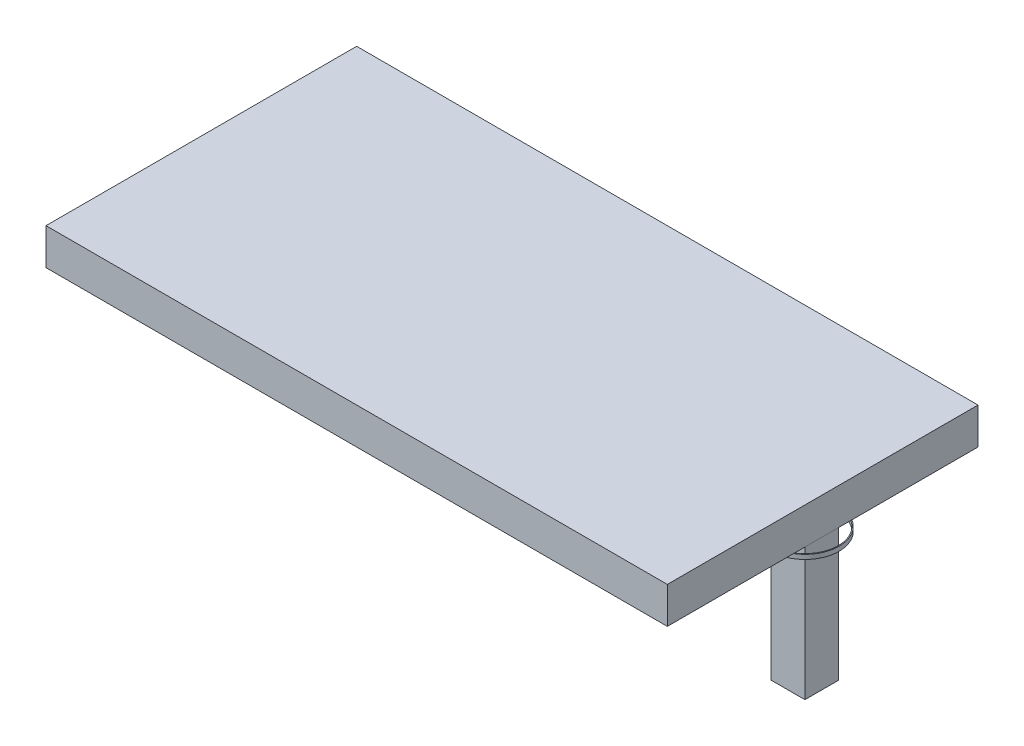
SolidWorks part; units mm, degrees
ref_plane "Front Plane" through (0, 0, 0) normal (0, 0, 1) x (1, 0, 0)
ref_plane "Top Plane" through (0, 0, 0) normal (0, 1, 0) x (1, 0, 0)
ref_plane "Right Plane" through (0, 0, 0) normal (1, 0, 0) x (0, 0, -1)
sketch "Sketch1" plane through (0, 0, 0) normal (0, 1, 0) x (1, 0, 0)
  line L1 (-350, 175) -> (350, 175)
  line L2 (-350, 175) -> (-350, -175)
  line L3 (-350, -175) -> (350, -175)
  line L4 (350, 175) -> (350, -175)
  line L5 (-350, 175) -> (350, -175) construction
  line L6 (-350, -175) -> (350, 175) construction
  line L7 (-310, -135) -> (310, -135)
  line L8 (-310, -135) -> (-310, 135)
  line L9 (-310, 135) -> (310, 135)
  line L10 (310, -135) -> (310, 135)
  line L11 (-310, -135) -> (310, 135) construction
  line L12 (-310, 135) -> (310, -135) construction
  point P0 (0, 0)
  point P6 (0, 0)
  dimension "D1" = 700
  dimension "D2" = 350
  dimension "D3" = 40
  dimension "D4" = 40
extrude "Boss-Extrude1" add sketch "Sketch1" along normal blind 40
sketch "Sketch2" plane through (0, 40, 0) normal (0, 1, 0) x (1, 0, 0)
  line L4 (350, -175) -> (350, 175)
  line L5 (350, 175) -> (-350, 175)
  line L6 (-350, 175) -> (-350, -175)
  line L7 (-350, -175) -> (350, -175)
  line L8 (350, -175) -> (350, 175)
  line L9 (350, 175) -> (-350, 175)
  line L10 (-350, 175) -> (-350, -175)
  line L11 (-350, -175) -> (350, -175)
  dimension "D1" = 0
extrude "Boss-Extrude2" add sketch "Sketch2" along normal blind 1
sketch "Sketch3" plane through (0, 0, 0) normal (0, -1, 0) x (1, 0, 0)
  line L1 (-349, 19) -> (-311, 19)
  line L2 (-349, 19) -> (-349, -19)
  line L3 (-349, -19) -> (-311, -19)
  line L4 (-311, 19) -> (-311, -19)
  line L7 (0, 175) -> (0, -175) construction
  line L8 (-350, 175) -> (350, 175) construction
  line L9 (350, -175) -> (-350, -175) construction
  line L10 (349, 19) -> (349, -19)
  line L12 (-438.1379, 0) -> (410.6858, 0) construction
  line L13 (-350, -175) -> (-350, 175) construction
  line L14 (-310, -135) -> (-310, 135) construction
  line L15 (311, 19) -> (311, -19)
  line L16 (349, 19) -> (311, 19)
  line L17 (349, -19) -> (311, -19)
  dimension "D2" = 1
  dimension "D3" = 1
  dimension "D4" = 38
extrude "Boss-Extrude3" add sketch "Sketch3" along normal blind 150
sketch "Sketch4" plane through (0, 0, 0) normal (0, -1, 0) x (1, 0, 0)
  line L1 (-51, 154) -> (-32, 154)
  line L2 (-51, 154) -> (-51, 135)
  line L3 (-51, 135) -> (-32, 135)
  line L4 (-32, 154) -> (-32, 135)
  line L5 (-310, 135) -> (310, 135) construction
  line L6 (-350, -175) -> (-350, 175) construction
  dimension "D1" = 19
  dimension "D2" = 299
  dimension "D3" = 19
extrude "Boss-Extrude4" add sketch "Sketch4" along normal blind 20
sketch "Sketch5" plane through (0, 0, 0) normal (0, -1, 0) x (1, 0, 0)
  line L0 (0, 175) -> (0, -175) construction
  line L1 (-350, 175) -> (350, 175) construction
  line L2 (350, -175) -> (-350, -175) construction
  line L3 (-349, -19) -> (-311, -19) construction
  line L4 (-349, 19) -> (-349, -19) construction
  circle A0 centre (-330, 0) radius 37.5
  circle A1 centre (-330, 0) radius 38.5
  circle A2 centre (330, 0) radius 38.5
  circle A3 centre (330, 0) radius 37.5
  dimension "D1" = 75
  dimension "D2" = 19
  dimension "D3" = 19
  dimension "D4" = 1
extrude "Boss-Extrude5" add sketch "Sketch5" along normal blind 5
